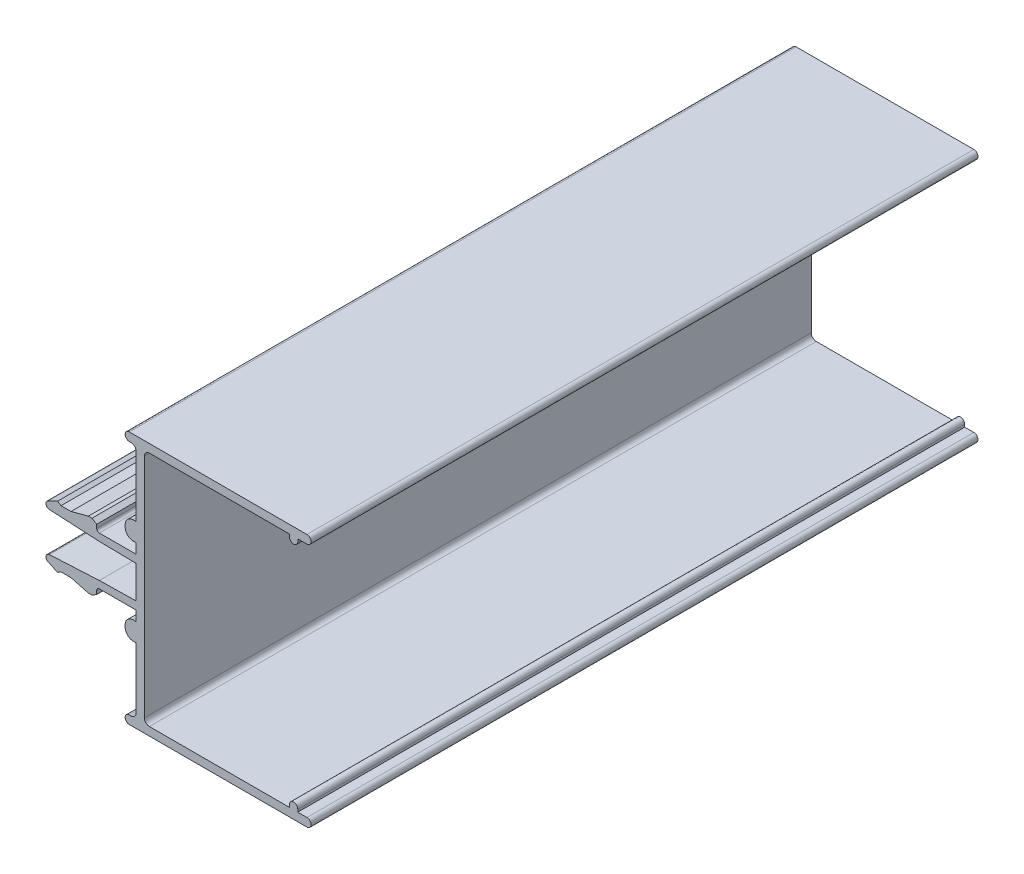
SolidWorks part; units mm, degrees
material "ABS"
ref_plane "Front" through (0, 0, 0) normal (0, 0, 1) x (1, 0, 0)
ref_plane "Top" through (0, 0, 0) normal (0, 1, 0) x (1, 0, 0)
ref_plane "Right" through (0, 0, 0) normal (1, 0, 0) x (0, 0, -1)
sketch "Sk Main Extrusion" plane through (0, 0, 0) normal (0, 0, 1) x (1, 0, 0)
  line L0 (-3.83, 2.5328) -> (-11.3125, 2.9251)
  line L1 (-3.83, -2.5328) -> (-11.3125, -2.9251)
  line L2 (1.1989, -5.1201) -> (1.67, -5.1201)
  line L3 (1.1989, -7.8799) -> (1.67, -7.8799)
  line L4 (1.1989, 7.8799) -> (1.67, 7.8799)
  line L5 (1.1989, 5.1201) -> (1.67, 5.1201)
  line L6 (1.67, -5.1201) -> (1.67, -7.8799) construction
  line L7 (1.67, -7.8799) -> (1.67, -17)
  line L8 (0.92, 17.75) -> (0.663, 17.75)
  line L9 (0.663, -17.75) -> (0.663, -19) construction
  line L10 (1.67, 7.8799) -> (1.67, 5.1201) construction
  line L11 (0, 0) -> (1.67, 0) construction
  line L12 (0.663, 19) -> (27.295, 19)
  line L13 (1.67, 17) -> (1.67, 7.8799)
  line L14 (0.663, 19) -> (0.663, 17.75) construction
  line L15 (1.67, 17) -> (2.92, 17) construction
  line L16 (3.67, 17.75) -> (24.67, 17.75)
  line L17 (25.92, 17.75) -> (27.295, 17.75)
  line L18 (0.663, -19) -> (27.295, -19)
  line L19 (3.67, -17.75) -> (24.67, -17.75)
  line L20 (24.67, 17.75) -> (24.67, 17.375)
  line L21 (0.038, 6.5) -> (1.67, 6.5) construction
  line L22 (25.92, 17.75) -> (25.92, 17.375)
  line L23 (27.295, 19) -> (27.295, 17.75) construction
  line L24 (2.92, 0) -> (31.3744, 0) construction
  line L25 (24.67, -17.75) -> (24.67, -17.375)
  line L26 (25.92, -17.75) -> (25.92, -17.375)
  line L28 (25.92, -17.75) -> (27.295, -17.75)
  line L78 (0.038, 6.65) -> (0.038, 6.35)
  line L79 (1.67, 5.1201) -> (1.67, 3.625)
  line L80 (1.67, 3.625) -> (-3.83, 3.625)
  line L81 (-4.23, 4.025) -> (-4.23, 4.56)
  line L82 (-4.23, 4.56) -> (-4.9341, 5)
  line L83 (-4.9341, 5) -> (-5.4741, 5)
  line L84 (-5.4741, 5) -> (-8.08, 4.3)
  line L85 (-8.08, 4.3) -> (-9.58, 4.3)
  line L86 (-9.58, 4.3) -> (-10.1001, 4.625)
  line L87 (-10.1001, 4.625) -> (-11.5147, 3.9654)
  line L92 (-3.83, 2.5328) -> (1.67, 2.4368)
  line L93 (1.67, 2.4368) -> (1.67, -2.4368)
  line L94 (1.67, -2.4368) -> (-3.83, -2.5328)
  line L99 (-11.5147, -3.9654) -> (-10.1001, -4.625)
  line L100 (-10.1001, -4.625) -> (-9.58, -4.3)
  line L101 (-9.58, -4.3) -> (-8.08, -4.3)
  line L102 (-8.08, -4.3) -> (-5.4741, -5)
  line L103 (-5.4741, -5) -> (-4.9341, -5)
  line L104 (-4.9341, -5) -> (-4.23, -4.56)
  line L105 (-4.23, -4.56) -> (-4.23, -4.025)
  line L106 (-3.83, -3.625) -> (1.67, -3.625)
  line L107 (1.67, -3.625) -> (1.67, -5.1201)
  line L108 (0.038, -6.35) -> (0.038, -6.65)
  line L110 (0.92, -17.75) -> (0.663, -17.75)
  line L113 (2.92, -17) -> (2.92, 17)
  arc A0 (0.92, 17.75) -> (1.67, 17) centre (0.92, 17) cw
  arc A1 (0.663, 17.75) -> (0.663, 19) centre (0.663, 18.375) cw
  arc A2 (3.67, -17.75) -> (2.92, -17) centre (3.67, -17) cw
  arc A3 (0.663, -19) -> (0.663, -17.75) centre (0.663, -18.375) cw
  arc A4 (24.67, 17.375) -> (25.92, 17.375) centre (25.295, 17.375) ccw
  arc A5 (1.67, -17) -> (0.92, -17.75) centre (0.92, -17) cw
  arc A6 (27.295, -17.75) -> (27.295, -19) centre (27.295, -18.375) cw
  arc A7 (2.92, 17) -> (3.67, 17.75) centre (3.67, 17) cw
  arc A8 (27.295, 17.75) -> (27.295, 19) centre (27.295, 18.375) ccw
  arc A9 (24.67, -17.375) -> (25.92, -17.375) centre (25.295, -17.375) cw
  arc A54 (1.1989, 7.8799) -> (0.038, 6.65) centre (1.27, 6.65) ccw
  arc A55 (0.038, 6.35) -> (1.1989, 5.1201) centre (1.27, 6.35) ccw
  arc A58 (-4.23, 4.025) -> (-3.83, 3.625) centre (-3.83, 4.025) ccw
  arc A59 (-11.5147, 3.9654) -> (-11.3125, 2.9251) centre (-11.2839, 3.4704) ccw
  arc A66 (-11.3125, -2.9251) -> (-11.5147, -3.9654) centre (-11.2839, -3.4704) ccw
  arc A67 (-3.83, -3.625) -> (-4.23, -4.025) centre (-3.83, -4.025) ccw
  arc A70 (1.1989, -5.1201) -> (0.038, -6.35) centre (1.27, -6.35) ccw
  arc A71 (0.038, -6.65) -> (1.1989, -7.8799) centre (1.27, -6.65) ccw
  point P10 (-1.08, 3.625)
  point P58 (0, 0)
  point P59 (0.038, 18.375)
  point P61 (1.67, 0)
  point P74 (0.038, -18.375)
  dimension "D4" = 1.632
  dimension "D14" = 1.232
  dimension "D16" = 1.25
  dimension "D23" = 0.4
  dimension "D26" = 25
  dimension "D17" = 0.75
  dimension "D18" = 0.75
  dimension "D19" = 0.75
  dimension "D20" = 0.75
  dimension "D27" = 1
  dimension "D2" = 1.25
  dimension "D3" = 91
  dimension "D5" = 19
  dimension "D6" = 90
  dimension "D7" = 90
  dimension "D8" = 2.7599
  dimension "D9" = 91
  dimension "D10" = 1.67
  dimension "D11" = 2.4368
  dimension "D12" = 3.625
  dimension "D13" = 5.1201
  dimension "D15" = 0.3
  dimension "D21" = 0.4711
  dimension "D22" = 7.8799
  dimension "D24" = 0.4
  dimension "D25" = 38
  dimension "D28" = 2
extrude "Main Extrusion" add sketch "Sk Main Extrusion" against normal blind 100
equation "\"Weight kg\"= round ( \"SW-Mass\" , 2 )"
equation "\"Weight lbs\"= round ( \"SW-Mass\" * 2.2046 , 2 )"
equation "\"Length mm\"= round ( \"Length@Main Extrusion\" , 2 )"
equation "\"Length in\"= round ( \"Length@Main Extrusion\" / 25.4 , 3 )"
